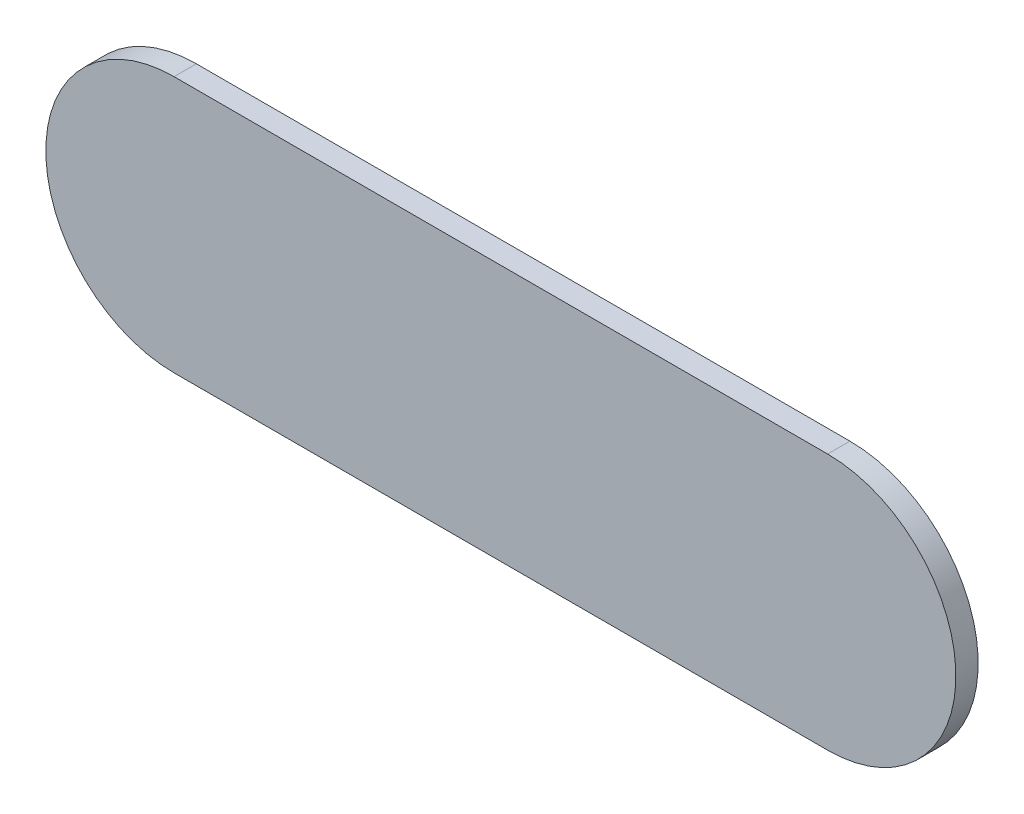
SolidWorks part; units mm, degrees
material "Polyurethane Foam Flexible"
ref_plane "Front Plane" through (0, 0, 0) normal (0, 0, 1) x (1, 0, 0)
ref_plane "Top Plane" through (0, 0, 0) normal (0, 1, 0) x (1, 0, 0)
ref_plane "Right Plane" through (0, 0, 0) normal (1, 0, 0) x (0, 0, -1)
sketch "Sketch1" plane through (0, 0, 0) normal (0, 0, 1) x (1, 0, 0)
  line L1 (-14.65, -5.75) -> (14.65, -5.75)
  line L3 (-14.65, 5.75) -> (14.65, 5.75)
  line L5 (-14.65, -5.75) -> (14.65, 5.75) construction
  line L6 (-14.65, 5.75) -> (14.65, -5.75) construction
  arc A0 (14.65, 5.75) -> (14.65, -5.75) centre (14.65, 0) cw
  arc A1 (-14.65, -5.75) -> (-14.65, 5.75) centre (-14.65, 0) cw
  point P0 (0, 0)
  dimension "D1" = 11.5
  dimension "D2" = 29.3
extrude "Boss-Extrude1" add sketch "Sketch1" along normal blind 1
